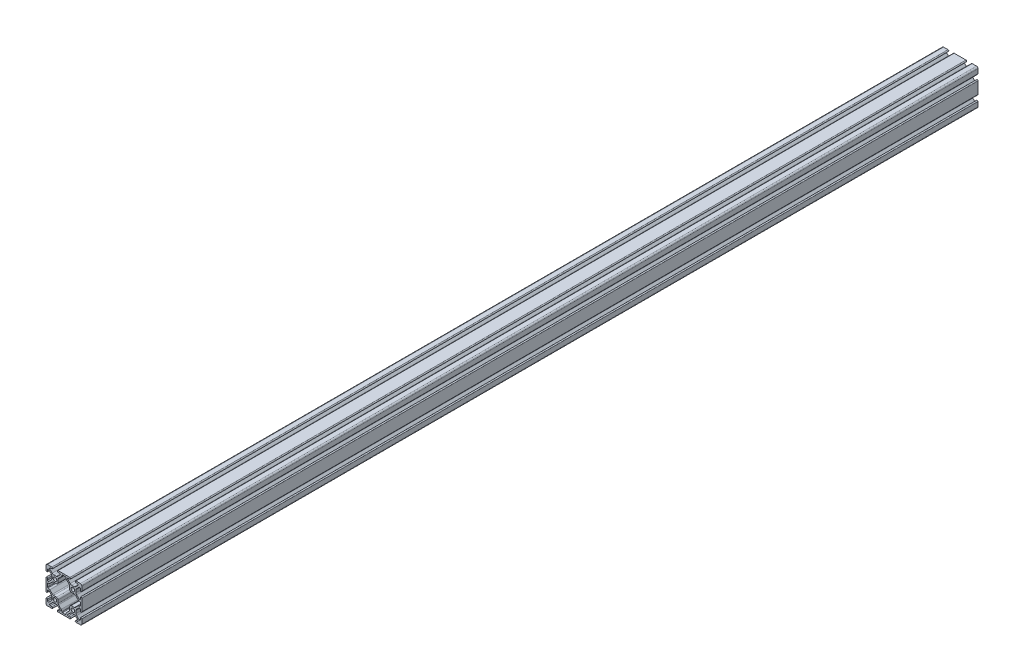
SolidWorks part; units mm, degrees
material "6061 Alloy"
ref_plane "Front Plane" through (0, 0, 0) normal (0, 0, 1) x (1, 0, 0)
ref_plane "Top Plane" through (0, 0, 0) normal (0, 1, 0) x (1, 0, 0)
ref_plane "Right Plane" through (0, 0, 0) normal (1, 0, 0) x (0, 0, -1)
ref_plane "Plane1" through (0, 0, -1500) normal (0, 0, -1) x (-1, 0, 0)
sketch "Sketch1" plane through (0, 0, -1500) normal (0, 0, -1) x (-1, 0, 0)
  line L0 (22.86, 2.1816) -> (22.86, -2.1816)
  line L1 (22.1, -2.9416) -> (21.85, -2.9416)
  line L2 (19.6226, -3.8642) -> (16.0341, -7.4527)
  line L3 (14.4714, -8.1) -> (10.31, -8.1)
  line L4 (8.1, -10.31) -> (8.1, -14.5087)
  line L5 (7.4791, -16.0077) -> (3.8502, -19.6365)
  line L6 (2.93, -21.8581) -> (2.93, -22.1)
  line L7 (2.17, -22.86) -> (-2.17, -22.86)
  line L8 (-2.93, -22.1) -> (-2.93, -21.8581)
  line L9 (-3.8502, -19.6365) -> (-7.4791, -16.0077)
  line L10 (-8.1, -14.5087) -> (-8.1, -10.31)
  line L11 (-10.31, -8.1) -> (-14.4714, -8.1)
  line L12 (-16.0341, -7.4527) -> (-19.6226, -3.8642)
  line L13 (-21.85, -2.9416) -> (-22.1, -2.9416)
  line L14 (-22.86, -2.1816) -> (-22.86, 2.1816)
  line L15 (-22.1, 2.9416) -> (-21.85, 2.9416)
  line L16 (-19.6226, 3.8642) -> (-16.0341, 7.4527)
  line L17 (-14.4714, 8.1) -> (-10.31, 8.1)
  line L18 (-8.1, 10.31) -> (-8.1, 14.5087)
  line L19 (-7.4791, 16.0077) -> (-3.8502, 19.6365)
  line L20 (-2.93, 21.8581) -> (-2.93, 22.1)
  line L21 (-2.17, 22.86) -> (2.17, 22.86)
  line L22 (2.93, 22.1) -> (2.93, 21.8581)
  line L23 (3.8502, 19.6365) -> (7.4791, 16.0077)
  line L24 (8.1, 14.5087) -> (8.1, 10.31)
  line L25 (10.31, 8.1) -> (14.4714, 8.1)
  line L26 (16.0341, 7.4527) -> (19.6226, 3.8642)
  line L27 (21.85, 2.9416) -> (22.1, 2.9416)
  line L28 (22.86, 8.18) -> (22.86, 6.0718)
  line L29 (21.1498, 5.3634) -> (17.8285, 8.6847)
  line L30 (16.9, 10.9263) -> (16.9, 14.0737)
  line L31 (17.8285, 16.3153) -> (21.1498, 19.6366)
  line L32 (22.86, 18.9282) -> (22.86, 16.82)
  line L33 (25, 16.82) -> (25, 23)
  line L34 (23, 25) -> (16.82, 25)
  line L35 (16.82, 22.86) -> (18.9282, 22.86)
  line L36 (19.6366, 21.1498) -> (16.3153, 17.8285)
  line L37 (14.0737, 16.9) -> (10.9263, 16.9)
  line L38 (8.6847, 17.8285) -> (5.3634, 21.1498)
  line L39 (6.0718, 22.86) -> (8.18, 22.86)
  line L40 (8.18, 25) -> (-8.18, 25)
  line L41 (-8.18, 22.86) -> (-6.0718, 22.86)
  line L42 (-5.3634, 21.1498) -> (-8.6847, 17.8285)
  line L43 (-10.9263, 16.9) -> (-14.0737, 16.9)
  line L44 (-16.3153, 17.8285) -> (-19.6366, 21.1498)
  line L45 (-18.9282, 22.86) -> (-16.82, 22.86)
  line L46 (-16.82, 25) -> (-23, 25)
  line L47 (-25, 23) -> (-25, 16.82)
  line L48 (-22.86, 16.82) -> (-22.86, 18.9282)
  line L49 (-21.1498, 19.6366) -> (-17.8285, 16.3153)
  line L50 (-16.9, 14.0737) -> (-16.9, 10.9263)
  line L51 (-17.8285, 8.6847) -> (-21.1498, 5.3634)
  line L52 (-22.86, 6.0718) -> (-22.86, 8.18)
  line L53 (-25, 8.18) -> (-25, -8.18)
  line L54 (-22.86, -8.18) -> (-22.86, -6.0718)
  line L55 (-21.1498, -5.3634) -> (-17.8285, -8.6847)
  line L56 (-16.9, -10.9263) -> (-16.9, -14.0737)
  line L57 (-17.8285, -16.3153) -> (-21.1498, -19.6366)
  line L58 (-22.86, -18.9282) -> (-22.86, -16.82)
  line L59 (-25, -16.82) -> (-25, -23)
  line L60 (-23, -25) -> (-16.82, -25)
  line L61 (-16.82, -22.86) -> (-18.9282, -22.86)
  line L62 (-19.6366, -21.1498) -> (-16.3153, -17.8285)
  line L63 (-14.0737, -16.9) -> (-10.9263, -16.9)
  line L64 (-8.6847, -17.8285) -> (-5.3634, -21.1498)
  line L65 (-6.0718, -22.86) -> (-8.18, -22.86)
  line L66 (-8.18, -25) -> (8.18, -25)
  line L67 (8.18, -22.86) -> (6.0718, -22.86)
  line L68 (5.3634, -21.1498) -> (8.6847, -17.8285)
  line L69 (10.9263, -16.9) -> (14.0737, -16.9)
  line L70 (16.3153, -17.8285) -> (19.6366, -21.1498)
  line L71 (18.9282, -22.86) -> (16.82, -22.86)
  line L72 (16.82, -25) -> (23, -25)
  line L73 (25, -23) -> (25, -16.82)
  line L74 (22.86, -16.82) -> (22.86, -18.9282)
  line L75 (21.1498, -19.6366) -> (17.8285, -16.3153)
  line L76 (16.9, -14.0737) -> (16.9, -10.9263)
  line L77 (17.8285, -8.6847) -> (21.1498, -5.3634)
  line L78 (22.86, -6.0718) -> (22.86, -8.18)
  line L79 (25, -8.18) -> (25, 8.18)
  arc A0 (22.86, -2.1816) -> (22.1, -2.9416) centre (22.1, -2.1816) cw
  arc A1 (21.85, -2.9416) -> (19.6226, -3.8642) centre (21.85, -6.0916) ccw
  arc A2 (16.0341, -7.4527) -> (14.4714, -8.1) centre (14.4714, -5.89) cw
  arc A3 (10.31, -8.1) -> (8.1, -10.31) centre (10.31, -10.31) ccw
  arc A4 (8.1, -14.5087) -> (7.4791, -16.0077) centre (5.98, -14.5087) cw
  arc A5 (3.8502, -19.6365) -> (2.93, -21.8581) centre (6.0719, -21.8581) ccw
  arc A6 (2.93, -22.1) -> (2.17, -22.86) centre (2.17, -22.1) cw
  arc A7 (-2.17, -22.86) -> (-2.93, -22.1) centre (-2.17, -22.1) cw
  arc A8 (-2.93, -21.8581) -> (-3.8502, -19.6365) centre (-6.0719, -21.8581) ccw
  arc A9 (-7.4791, -16.0077) -> (-8.1, -14.5087) centre (-5.98, -14.5087) cw
  arc A10 (-8.1, -10.31) -> (-10.31, -8.1) centre (-10.31, -10.31) ccw
  arc A11 (-14.4714, -8.1) -> (-16.0341, -7.4527) centre (-14.4714, -5.89) cw
  arc A12 (-19.6226, -3.8642) -> (-21.85, -2.9416) centre (-21.85, -6.0916) ccw
  arc A13 (-22.1, -2.9416) -> (-22.86, -2.1816) centre (-22.1, -2.1816) cw
  arc A14 (-22.86, 2.1816) -> (-22.1, 2.9416) centre (-22.1, 2.1816) cw
  arc A15 (-21.85, 2.9416) -> (-19.6226, 3.8642) centre (-21.85, 6.0916) ccw
  arc A16 (-16.0341, 7.4527) -> (-14.4714, 8.1) centre (-14.4714, 5.89) cw
  arc A17 (-10.31, 8.1) -> (-8.1, 10.31) centre (-10.31, 10.31) ccw
  arc A18 (-8.1, 14.5087) -> (-7.4791, 16.0077) centre (-5.98, 14.5087) cw
  arc A19 (-3.8502, 19.6365) -> (-2.93, 21.8581) centre (-6.0719, 21.8581) ccw
  arc A20 (-2.93, 22.1) -> (-2.17, 22.86) centre (-2.17, 22.1) cw
  arc A21 (2.17, 22.86) -> (2.93, 22.1) centre (2.17, 22.1) cw
  arc A22 (2.93, 21.8581) -> (3.8502, 19.6365) centre (6.0719, 21.8581) ccw
  arc A23 (7.4791, 16.0077) -> (8.1, 14.5087) centre (5.98, 14.5087) cw
  arc A24 (8.1, 10.31) -> (10.31, 8.1) centre (10.31, 10.31) ccw
  arc A25 (14.4714, 8.1) -> (16.0341, 7.4527) centre (14.4714, 5.89) cw
  arc A26 (19.6226, 3.8642) -> (21.85, 2.9416) centre (21.85, 6.0916) ccw
  arc A27 (22.1, 2.9416) -> (22.86, 2.1816) centre (22.1, 2.1816) cw
  circle A28 centre (12.5, 12.5) radius 2.5
  circle A29 centre (12.5, -12.5) radius 2.5
  circle A30 centre (-12.5, 12.5) radius 2.5
  circle A31 centre (-12.5, -12.5) radius 2.5
  arc A32 (25, 8.18) -> (22.86, 8.18) centre (23.93, 8.18) ccw
  arc A33 (22.86, 6.0718) -> (21.1498, 5.3634) centre (21.8582, 6.0718) cw
  arc A34 (17.8285, 8.6847) -> (16.9, 10.9263) centre (20.07, 10.9263) cw
  arc A35 (16.9, 14.0737) -> (17.8285, 16.3153) centre (20.07, 14.0737) cw
  arc A36 (21.1498, 19.6366) -> (22.86, 18.9282) centre (21.8582, 18.9282) cw
  arc A37 (22.86, 16.82) -> (25, 16.82) centre (23.93, 16.82) ccw
  arc A38 (25, 23) -> (23, 25) centre (23, 23) ccw
  arc A39 (16.82, 25) -> (16.82, 22.86) centre (16.82, 23.93) ccw
  arc A40 (18.9282, 22.86) -> (19.6366, 21.1498) centre (18.9282, 21.8582) cw
  arc A41 (16.3153, 17.8285) -> (14.0737, 16.9) centre (14.0737, 20.07) cw
  arc A42 (10.9263, 16.9) -> (8.6847, 17.8285) centre (10.9263, 20.07) cw
  arc A43 (5.3634, 21.1498) -> (6.0718, 22.86) centre (6.0718, 21.8582) cw
  arc A44 (8.18, 22.86) -> (8.18, 25) centre (8.18, 23.93) ccw
  arc A45 (-8.18, 25) -> (-8.18, 22.86) centre (-8.18, 23.93) ccw
  arc A46 (-6.0718, 22.86) -> (-5.3634, 21.1498) centre (-6.0718, 21.8582) cw
  arc A47 (-8.6847, 17.8285) -> (-10.9263, 16.9) centre (-10.9263, 20.07) cw
  arc A48 (-14.0737, 16.9) -> (-16.3153, 17.8285) centre (-14.0737, 20.07) cw
  arc A49 (-19.6366, 21.1498) -> (-18.9282, 22.86) centre (-18.9282, 21.8582) cw
  arc A50 (-16.82, 22.86) -> (-16.82, 25) centre (-16.82, 23.93) ccw
  arc A51 (-23, 25) -> (-25, 23) centre (-23, 23) ccw
  arc A52 (-25, 16.82) -> (-22.86, 16.82) centre (-23.93, 16.82) ccw
  arc A53 (-22.86, 18.9282) -> (-21.1498, 19.6366) centre (-21.8582, 18.9282) cw
  arc A54 (-17.8285, 16.3153) -> (-16.9, 14.0737) centre (-20.07, 14.0737) cw
  arc A55 (-16.9, 10.9263) -> (-17.8285, 8.6847) centre (-20.07, 10.9263) cw
  arc A56 (-21.1498, 5.3634) -> (-22.86, 6.0718) centre (-21.8582, 6.0718) cw
  arc A57 (-22.86, 8.18) -> (-25, 8.18) centre (-23.93, 8.18) ccw
  arc A58 (-25, -8.18) -> (-22.86, -8.18) centre (-23.93, -8.18) ccw
  arc A59 (-22.86, -6.0718) -> (-21.1498, -5.3634) centre (-21.8582, -6.0718) cw
  arc A60 (-17.8285, -8.6847) -> (-16.9, -10.9263) centre (-20.07, -10.9263) cw
  arc A61 (-16.9, -14.0737) -> (-17.8285, -16.3153) centre (-20.07, -14.0737) cw
  arc A62 (-21.1498, -19.6366) -> (-22.86, -18.9282) centre (-21.8582, -18.9282) cw
  arc A63 (-22.86, -16.82) -> (-25, -16.82) centre (-23.93, -16.82) ccw
  arc A64 (-25, -23) -> (-23, -25) centre (-23, -23) ccw
  arc A65 (-16.82, -25) -> (-16.82, -22.86) centre (-16.82, -23.93) ccw
  arc A66 (-18.9282, -22.86) -> (-19.6366, -21.1498) centre (-18.9282, -21.8582) cw
  arc A67 (-16.3153, -17.8285) -> (-14.0737, -16.9) centre (-14.0737, -20.07) cw
  arc A68 (-10.9263, -16.9) -> (-8.6847, -17.8285) centre (-10.9263, -20.07) cw
  arc A69 (-5.3634, -21.1498) -> (-6.0718, -22.86) centre (-6.0718, -21.8582) cw
  arc A70 (-8.18, -22.86) -> (-8.18, -25) centre (-8.18, -23.93) ccw
  arc A71 (8.18, -25) -> (8.18, -22.86) centre (8.18, -23.93) ccw
  arc A72 (6.0718, -22.86) -> (5.3634, -21.1498) centre (6.0718, -21.8582) cw
  arc A73 (8.6847, -17.8285) -> (10.9263, -16.9) centre (10.9263, -20.07) cw
  arc A74 (14.0737, -16.9) -> (16.3153, -17.8285) centre (14.0737, -20.07) cw
  arc A75 (19.6366, -21.1498) -> (18.9282, -22.86) centre (18.9282, -21.8582) cw
  arc A76 (16.82, -22.86) -> (16.82, -25) centre (16.82, -23.93) ccw
  arc A77 (23, -25) -> (25, -23) centre (23, -23) ccw
  arc A78 (25, -16.82) -> (22.86, -16.82) centre (23.93, -16.82) ccw
  arc A79 (22.86, -18.9282) -> (21.1498, -19.6366) centre (21.8582, -18.9282) cw
  arc A80 (17.8285, -16.3153) -> (16.9, -14.0737) centre (20.07, -14.0737) cw
  arc A81 (16.9, -10.9263) -> (17.8285, -8.6847) centre (20.07, -10.9263) cw
  arc A82 (21.1498, -5.3634) -> (22.86, -6.0718) centre (21.8582, -6.0718) cw
  arc A83 (22.86, -8.18) -> (25, -8.18) centre (23.93, -8.18) ccw
extrude "Boss-Extrude1" add sketch "Sketch1" against normal blind 1250
